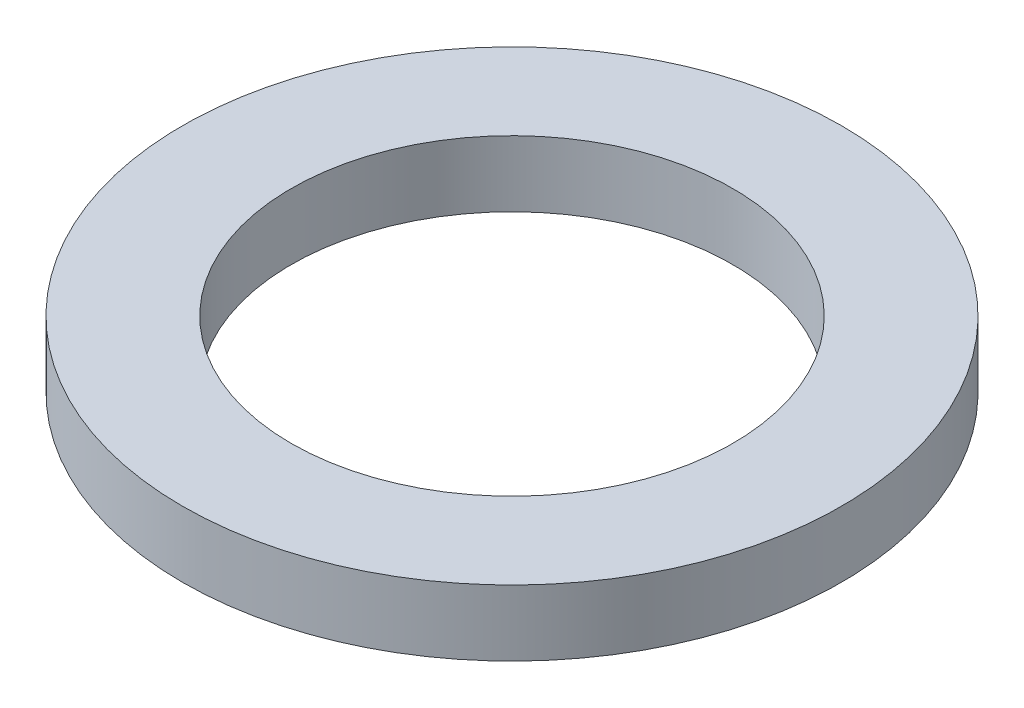
SolidWorks part; units mm, degrees
material "1.6523 (20NiCrMoS2-2)"
ref_plane "Front Plane" through (0, 0, 0) normal (0, 0, 1) x (1, 0, 0)
ref_plane "Top Plane" through (0, 0, 0) normal (0, 1, 0) x (1, 0, 0)
ref_plane "Right Plane" through (0, 0, 0) normal (1, 0, 0) x (0, 0, -1)
sketch "Sketch1" plane through (0, 0, 0) normal (0, 1, 0) x (1, 0, 0)
  circle A0 centre (0, 0) radius 5
  circle A1 centre (0, 0) radius 3.35
  dimension "D1" = 10
  dimension "D2" = 6.7
extrude "Boss-Extrude1" add sketch "Sketch1" along normal blind 1
